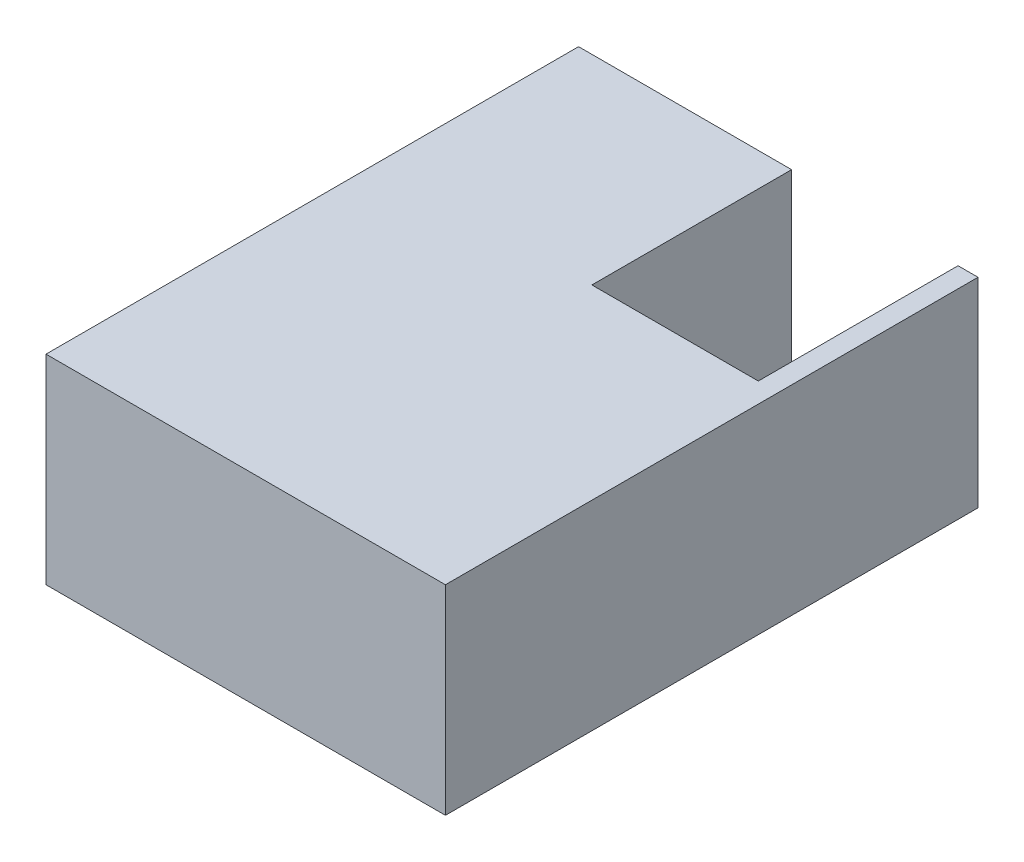
SolidWorks part; units mm, degrees
ref_plane "Front" through (0, 0, 0) normal (0, 0, 1) x (1, 0, 0)
ref_plane "Top" through (0, 0, 0) normal (0, 1, 0) x (1, 0, 0)
ref_plane "Right" through (0, 0, 0) normal (1, 0, 0) x (0, 0, -1)
sketch "Sketch1" plane through (0, 0, 0) normal (0, 1, 0) x (1, 0, 0)
  line L1 (0, 0) -> (600, 0)
  line L2 (0, 0) -> (0, -800)
  line L3 (0, -800) -> (600, -800)
  line L4 (600, 0) -> (600, -800)
  dimension "D1" = 800
  dimension "D2" = 600
extrude "Boss-Extrude1" add sketch "Sketch1" along normal blind 300
sketch "Sketch2" plane through (0, 300, 0) normal (0, 1, 0) x (1, 0, 0)
  line L0 (600, 0) -> (0, 0) construction
  line L1 (570, 0) -> (320, 0)
  line L2 (570, 0) -> (570, -300)
  line L3 (570, -300) -> (320, -300)
  line L4 (320, 0) -> (320, -300)
  line L5 (600, -800) -> (600, 0) construction
  dimension "D1" = 250
  dimension "D2" = 300
  dimension "D3" = 30
extrude "Cut-Extrude1" cut sketch "Sketch2" against normal through all
